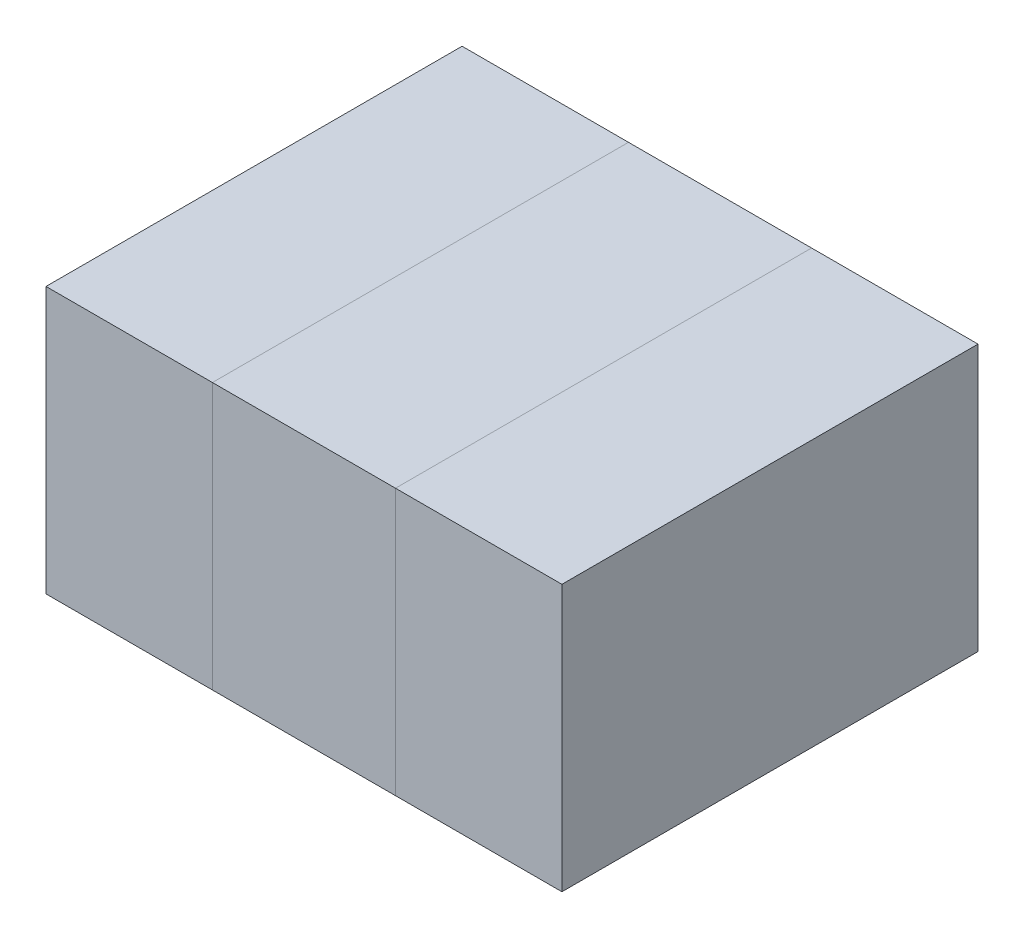
SolidWorks part; units mm, degrees
ref_plane "Front Plane" through (0, 0, 0) normal (0, 0, 1) x (1, 0, 0)
ref_plane "Top Plane" through (0, 0, 0) normal (0, 1, 0) x (1, 0, 0)
ref_plane "Right Plane" through (0, 0, 0) normal (1, 0, 0) x (0, 0, -1)
sketch "Sketch1" plane through (0, 0, 0) normal (0, 1, 0) x (1, 0, 0)
  line L1 (-0.275, -0.625) -> (0.275, -0.625)
  line L2 (-0.275, -0.625) -> (-0.275, 0.625)
  line L3 (-0.275, 0.625) -> (0.275, 0.625)
  line L4 (0.275, -0.625) -> (0.275, 0.625)
  line L5 (-0.275, -0.625) -> (0.275, 0.625) construction
  line L6 (-0.275, 0.625) -> (0.275, -0.625) construction
  point P0 (0, 0)
  dimension "D1" = 0.55
  dimension "D2" = 1.25
extrude "Boss-Extrude1" add sketch "Sketch1" along normal blind 0.8
sketch "Sketch2" plane through (0, 0, 0) normal (0, 1, 0) x (1, 0, 0)
  line L0 (0, 0.625) -> (0, -0.625) construction
  line L1 (-0.275, 0.625) -> (-0.775, 0.625)
  line L2 (-0.275, 0.625) -> (-0.275, -0.625)
  line L3 (-0.275, -0.625) -> (-0.775, -0.625)
  line L4 (-0.775, 0.625) -> (-0.775, -0.625)
  line L5 (0.275, 0.625) -> (-0.275, 0.625) construction
  line L6 (-0.275, -0.625) -> (0.275, -0.625) construction
  line L7 (0.275, -0.625) -> (0.775, -0.625)
  line L8 (0.775, 0.625) -> (0.775, -0.625)
  line L9 (0.275, 0.625) -> (0.775, 0.625)
  line L10 (0.275, 0.625) -> (0.275, -0.625)
  dimension "D1" = 1.25
  dimension "D2" = 0.5
extrude "Boss-Extrude2" add sketch "Sketch2" along normal blind 0.8 separate body
